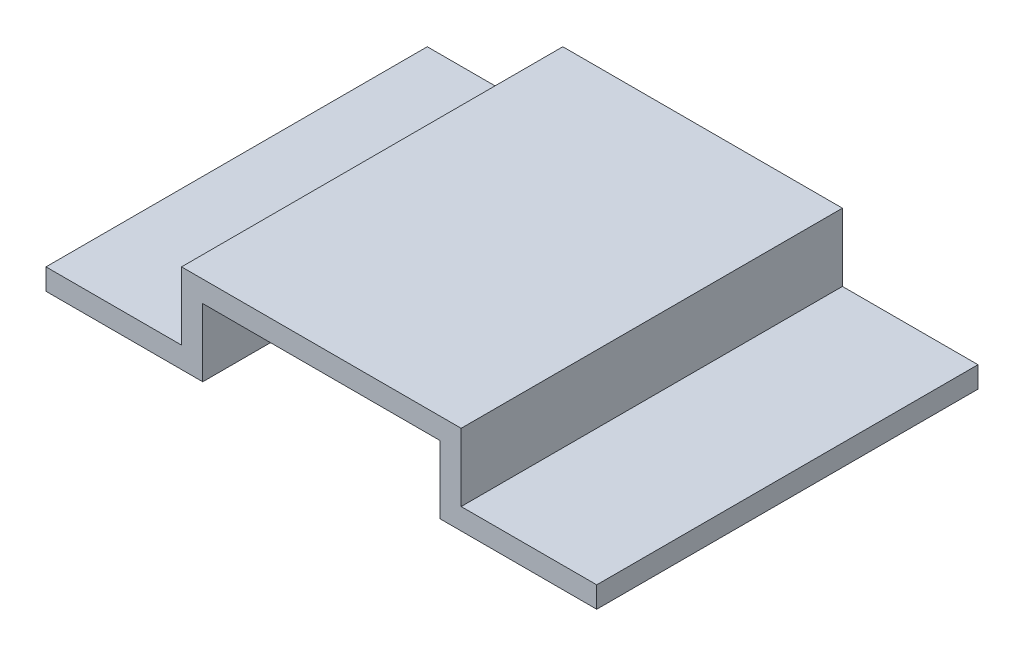
SolidWorks part; units mm, degrees
ref_plane "Front Plane" through (0, 0, 0) normal (0, 0, 1) x (1, 0, 0)
ref_plane "Top Plane" through (0, 0, 0) normal (0, 1, 0) x (1, 0, 0)
ref_plane "Right Plane" through (0, 0, 0) normal (1, 0, 0) x (0, 0, -1)
sketch "Sketch1" plane through (0, 0, 0) normal (0, 0, 1) x (1, 0, 0)
  line L0 (50, 0) -> (235, 0)
  line L1 (235, 0) -> (235, 80)
  line L2 (235, 80) -> (515, 80)
  line L6 (50, 25) -> (210, 25)
  line L7 (210, 25) -> (210, 105)
  line L8 (210, 105) -> (540, 105)
  line L12 (375, 105) -> (375, 80) construction
  line L18 (50, 25) -> (50, 0)
  line L19 (700, 25) -> (700, 0)
  line L20 (540, 25) -> (540, 105)
  line L21 (700, 25) -> (540, 25)
  line L22 (515, 0) -> (515, 80)
  line L23 (700, 0) -> (515, 0)
  dimension "D1" = 25
  dimension "D2" = 375
  dimension "D3" = 25
  dimension "D4" = 25
  dimension "D5" = 140
  dimension "D6" = 80
  dimension "D7" = 50
extrude "Boss-Extrude1" add sketch "Sketch1" along normal blind 450 contours L8 L20 L21 L19 L23 L22 L2 L1 L0 L18 L6 L7
